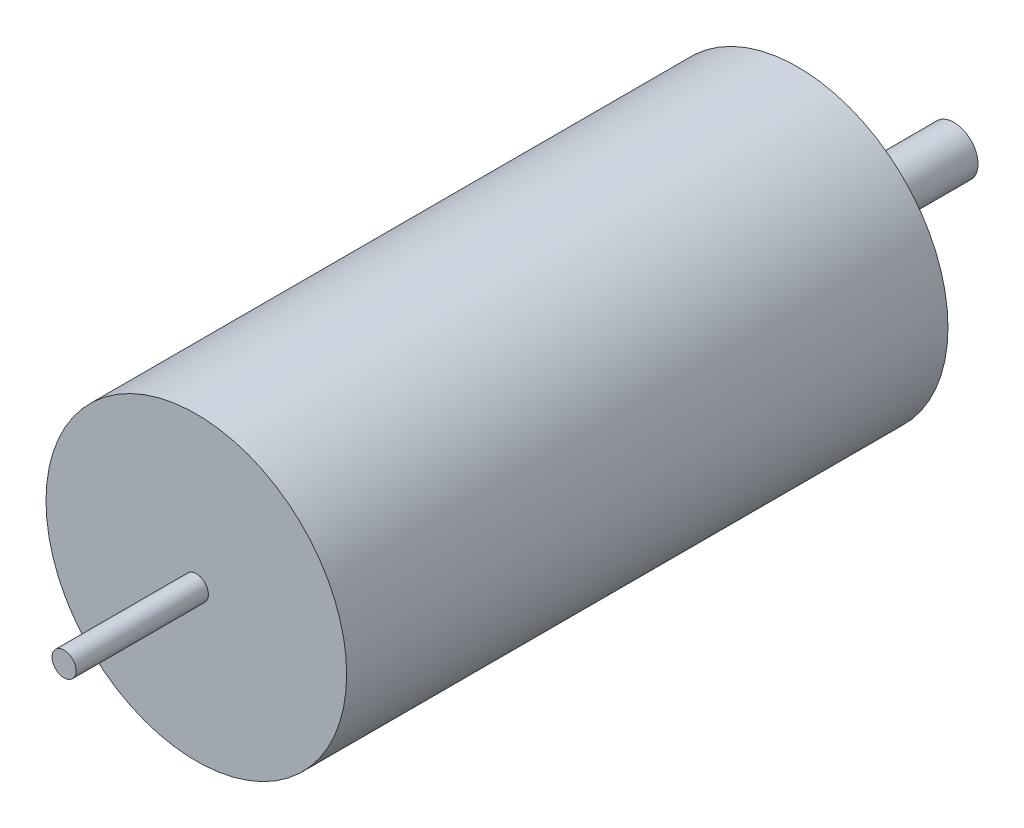
SolidWorks part; units mm, degrees
material "Chrome Stainless Steel"
ref_plane "Front Plane" through (0, 0, 0) normal (0, 0, 1) x (1, 0, 0)
ref_plane "Top Plane" through (0, 0, 0) normal (0, 1, 0) x (1, 0, 0)
ref_plane "Right Plane" through (0, 0, 0) normal (1, 0, 0) x (0, 0, -1)
sketch "Sketch1" plane through (0, 0, 0) normal (0, 0, 1) x (1, 0, 0)
  circle A0 centre (0, 0) radius 12.5
  dimension "D1" = 25
extrude "Boss-Extrude1" add sketch "Sketch1" along normal blind 50
sketch "Sketch2" plane through (0, 0, 0) normal (0, 0, -1) x (-1, 0, 0)
  circle A0 centre (0, 0) radius 3.5
  dimension "D1" = 7
extrude "Boss-Extrude2" add sketch "Sketch2" along normal blind 2
sketch "Sketch3" plane through (0, 0, -2) normal (0, 0, -1) x (-1, 0, 0)
  circle A0 centre (0, 0) radius 2
  dimension "D1" = 4
extrude "Boss-Extrude3" add sketch "Sketch3" along normal blind 11
sketch "Sketch4" plane through (0, 0, 0) normal (0, 0, -1) x (-1, 0, 0)
  line L0 (0, 13.2455) -> (0, -13.4561) construction
  circle A0 centre (-8.5, 0) radius 1.5
  circle A1 centre (0, 0) radius 3.5 construction
  circle A3 centre (8.5, 0) radius 1.5
  dimension "D1" = 3
  dimension "D2" = 17
extrude "Cut-Extrude1" cut sketch "Sketch4" against normal blind 5
sketch "Sketch5" plane through (0, 0, 50) normal (0, 0, 1) x (1, 0, 0)
  circle A0 centre (0, 0) radius 1
  dimension "D1" = 2
extrude "Boss-Extrude4" add sketch "Sketch5" along normal blind 11
